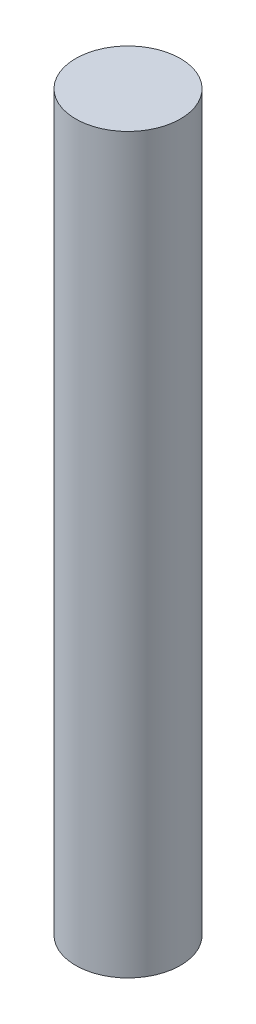
SolidWorks part; units mm, degrees
ref_plane "Front Plane" through (0, 0, 0) normal (0, 0, 1) x (1, 0, 0)
ref_plane "Top Plane" through (0, 0, 0) normal (0, 1, 0) x (1, 0, 0)
ref_plane "Right Plane" through (0, 0, 0) normal (1, 0, 0) x (0, 0, -1)
sketch "Sketch1" plane through (0, 0, 0) normal (0, 0, 1) x (1, 0, 0)
  line L1 (0, 0) -> (7.5, 0)
  line L2 (0, 0) -> (0, 105)
  line L3 (0, 105) -> (7.5, 105)
  line L4 (7.5, 0) -> (7.5, 105)
  dimension "D1" = 7.5
  dimension "D2" = 105
revolve "Revolve1" add sketch "Sketch1" angle 360 about L2
